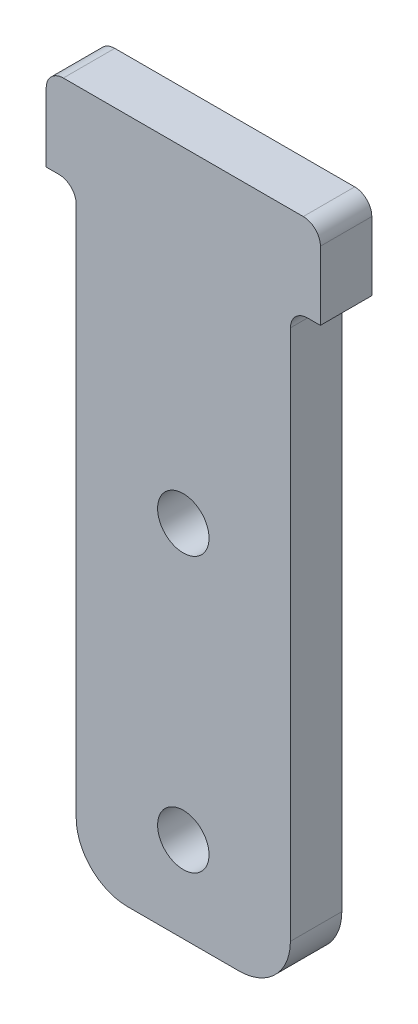
SolidWorks part; units mm, degrees
material "ABS"
ref_plane "Front Plane" through (0, 0, 0) normal (0, 0, 1) x (1, 0, 0)
ref_plane "Top Plane" through (0, 0, 0) normal (0, 1, 0) x (1, 0, 0)
ref_plane "Right Plane" through (0, 0, 0) normal (1, 0, 0) x (0, 0, -1)
sketch "Sketch1" plane through (0, 0, 0) normal (0, 0, 1) x (1, 0, 0)
  line L21 (6.25, 17.5) -> (8, 17.5)
  line L22 (-8, 22.5) -> (8, 22.5)
  line L23 (-8, 22.5) -> (-8, 17.5)
  line L24 (-8, 17.5) -> (-6.25, 17.5)
  line L25 (8, 22.5) -> (8, 17.5)
  line L26 (-8, 22.5) -> (8, 17.5) construction
  line L27 (-8, 17.5) -> (8, 22.5) construction
  line L29 (-6.25, 17.5) -> (-6.25, -17.5)
  line L30 (-6.25, -17.5) -> (6.25, -17.5)
  line L31 (6.25, 17.5) -> (6.25, -17.5)
  line L32 (-6.25, 17.5) -> (6.25, -17.5) construction
  line L33 (-6.25, -17.5) -> (6.25, 17.5) construction
  circle A10 centre (0, 3.5) radius 1.5
  circle A11 centre (0, -12.5) radius 1.5
  point P0 (0, -17.5)
  point P16 (0, 20)
  point P43 (0, 0)
  dimension "D17" = 3
  dimension "D13" = 16
  dimension "D14" = 5
  dimension "D15" = 35
  dimension "D16" = 12.5
  dimension "D18" = 16
  dimension "D19" = 5
extrude "Boss-Extrude1" add sketch "Sketch1" along normal blind 3
fillet "Fillet1" radius 1 4 edges at (-8, 22.5, 1.5) (8, 22.5, 1.5) (6.25, 17.5, 1.5) (-6.25, 17.5, 1.5)
fillet "Fillet2" radius 3 2 edges at (6.25, -17.5, 1.5) (-6.25, -17.5, 1.5)
